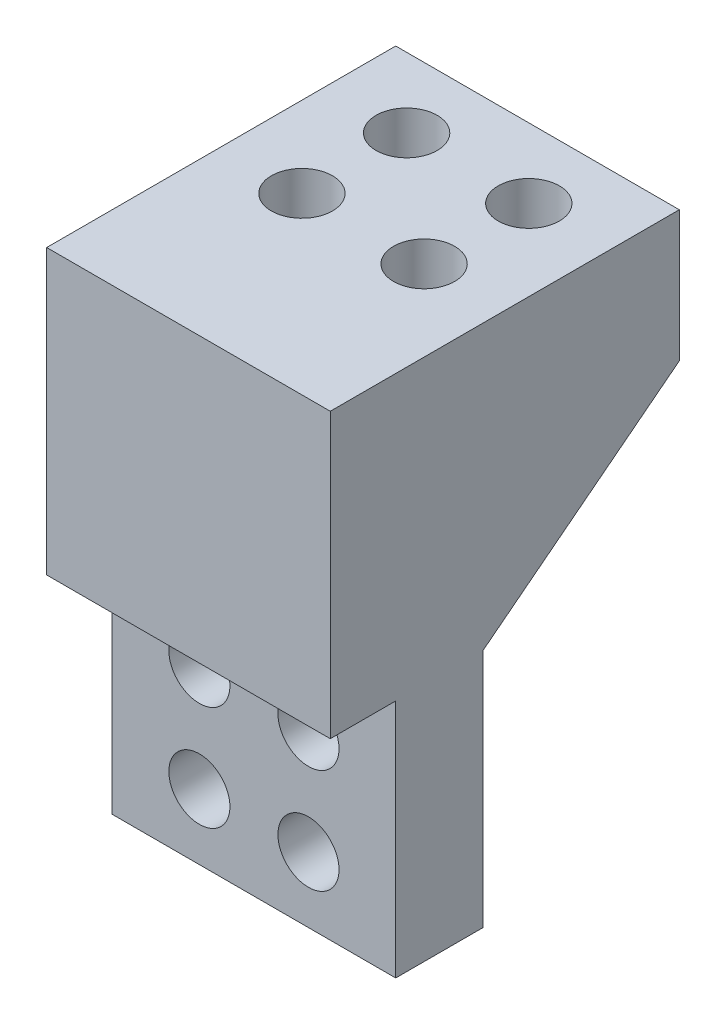
SolidWorks part; units mm, degrees
ref_plane "Alzado" through (0, 0, 0) normal (0, 0, 1) x (1, 0, 0)
ref_plane "Planta" through (0, 0, 0) normal (0, 1, 0) x (1, 0, 0)
ref_plane "Vista lateral" through (0, 0, 0) normal (1, 0, 0) x (0, 0, -1)
sketch "Croquis1" plane through (0, 0, 0) normal (0, 0, 1) x (1, 0, 0)
  line L1 (-32.5, -60) -> (32.5, -60)
  line L2 (-32.5, -60) -> (-32.5, 60)
  line L3 (-32.5, 60) -> (32.5, 60)
  line L4 (32.5, -60) -> (32.5, 60)
  line L5 (-32.5, -60) -> (32.5, 60) construction
  line L6 (-32.5, 60) -> (32.5, -60) construction
  point P0 (0, 0)
  dimension "D1" = 65
  dimension "D2" = 120
extrude "Saliente-Extruir1" add sketch "Croquis1" along normal blind 80
sketch "Croquis2" plane through (32.5, 0, 0) normal (1, 0, 0) x (0, 0, -1)
  line L0 (-80, -5) -> (-65, -5)
  line L1 (-80, -60) -> (-80, 60) construction
  line L2 (-65, -5) -> (-65, -60)
  line L3 (-80, -60) -> (0, -60) construction
  line L4 (-65, -60) -> (-80, -60)
  line L5 (-80, -60) -> (-80, -5)
  line L6 (-45, -60) -> (-45, -5)
  line L7 (-45, -60) -> (0, -60)
  line L8 (0, -60) -> (0, 30)
  line L9 (0, -60) -> (0, 60) construction
  line L10 (-45, -5) -> (0, 30)
  dimension "D1" = 55
  dimension "D2" = 15
  dimension "D3" = 30
  dimension "D4" = 20
extrude "Cortar-Extruir1" cut sketch "Croquis2" against normal blind 80
sketch "Croquis3" plane through (0, 0, 65) normal (0, 0, 1) x (1, 0, 0)
  line L0 (-32.5, -60) -> (32.5, -60) construction
  line L2 (0, -5) -> (0, -60) construction
  line L3 (-32.5, -5) -> (32.5, -5) construction
  circle A0 centre (-12.5, -21) radius 7
  circle A1 centre (-12.5, -45) radius 7
  circle A2 centre (12.5, -21) radius 7
  circle A3 centre (12.5, -45) radius 7
  dimension "D2" = 24
  dimension "D5" = 12.5
  dimension "D6" = 12.5
  dimension "D7" = 14
  dimension "D8" = 14
  dimension "D9" = 14
  dimension "D10" = 14
  dimension "D1" = 15
  dimension "D3" = 12.5
  dimension "D4" = 12.5
extrude "Cortar-Extruir2" cut sketch "Croquis3" against normal up to surface (20 mm away) up to face at (0, -32.5, 45)
sketch "Croquis4" plane through (0, 60, 0) normal (0, 1, 0) x (1, 0, 0)
  line L0 (0, -80) -> (0, 0) construction
  line L1 (32.5, -80) -> (-32.5, -80) construction
  line L2 (32.5, 0) -> (-32.5, 0) construction
  circle A0 centre (14, -16) radius 7
  circle A1 centre (-14, -16) radius 7
  circle A2 centre (14, -40) radius 7
  circle A3 centre (-14, -40) radius 7
  dimension "D3" = 14
  dimension "D6" = 14
  dimension "D7" = 24
  dimension "D8" = 14
  dimension "D9" = 14
  dimension "D10" = 24
  dimension "D1" = 14
  dimension "D2" = 16
  dimension "D4" = 14
  dimension "D5" = 16
extrude "Cortar-Extruir3" cut sketch "Croquis4" against normal blind 10
